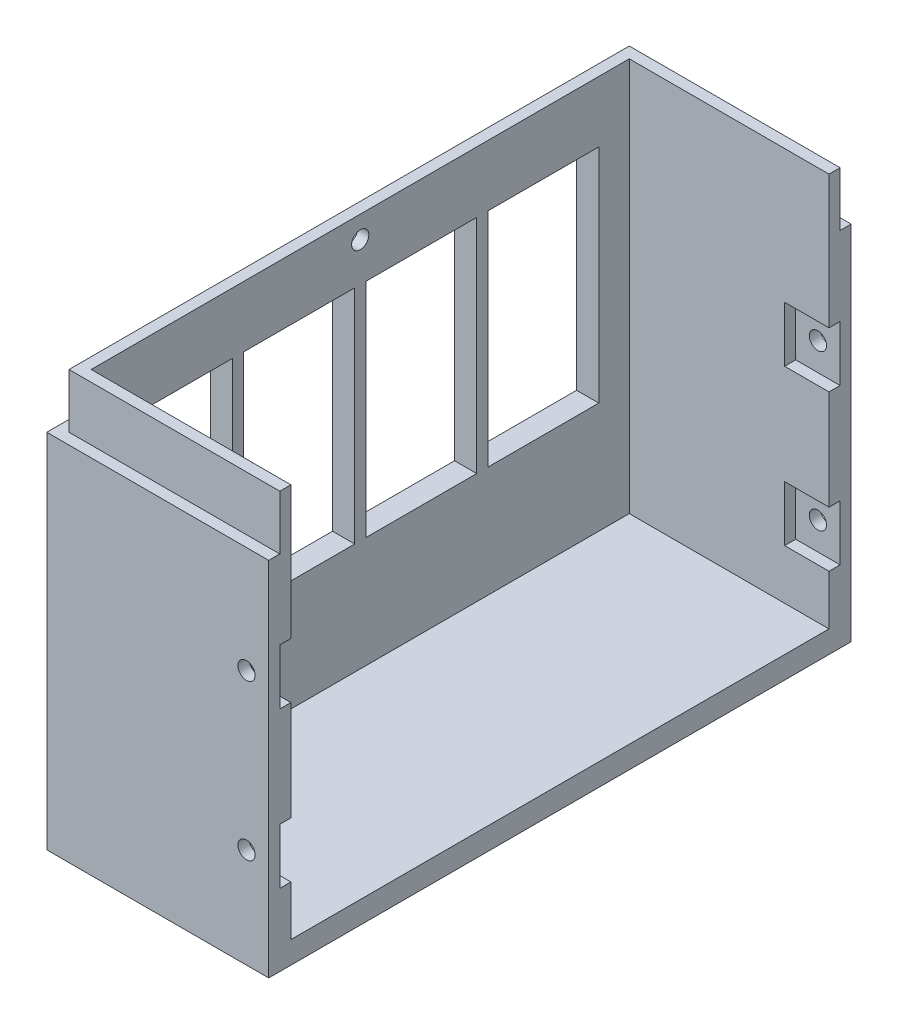
SolidWorks part; units mm, degrees
ref_plane "Front Plane" through (0, 0, 0) normal (0, 0, 1) x (1, 0, 0)
ref_plane "Top Plane" through (0, 0, 0) normal (0, 1, 0) x (1, 0, 0)
ref_plane "Right Plane" through (0, 0, 0) normal (1, 0, 0) x (0, 0, -1)
sketch "Sketch1" plane through (0, 0, 0) normal (0, 1, 0) x (1, 0, 0)
  line L1 (-20, 52.5) -> (20, 52.5)
  line L2 (-20, 52.5) -> (-20, -52.5)
  line L3 (-20, -52.5) -> (20, -52.5)
  line L4 (20, 52.5) -> (20, -52.5)
  line L5 (-20, 52.5) -> (20, -52.5) construction
  line L6 (-20, -52.5) -> (20, 52.5) construction
  point P0 (0, 0)
  dimension "D1" = 105
  dimension "D2" = 40
extrude "Boss-Extrude3" add sketch "Sketch1" along normal blind 75
sketch "Sketch4" plane through (20, 0, 0) normal (1, 0, 0) x (0, 0, -1)
  line L0 (-52.5, 75) -> (52.5, 75) construction
  line L1 (-48.5, 75) -> (48.5, 75)
  line L2 (-48.5, 75) -> (-48.5, 4)
  line L3 (-48.5, 4) -> (48.5, 4)
  line L4 (48.5, 75) -> (48.5, 4)
  line L5 (-52.5, 75) -> (-52.5, 0) construction
  line L6 (-52.5, 0) -> (52.5, 0) construction
  line L7 (52.5, 75) -> (52.5, 0) construction
  dimension "D1" = 4
  dimension "D2" = 4
  dimension "D3" = 4
extrude "Cut-Extrude2" cut sketch "Sketch4" against normal blind 36
sketch "Sketch5" plane through (0, 0, 52.5) normal (0, 0, 1) x (1, 0, 0)
  line L0 (-20, 75) -> (-20, 0) construction
  line L1 (20, 75) -> (-20, 75)
  line L2 (20, 75) -> (20, 65.2)
  line L3 (20, 65.2) -> (-20, 65.2)
  line L4 (-20, 75) -> (-20, 65.2)
  dimension "D1" = 9.8
extrude "Cut-Extrude3" cut sketch "Sketch5" against normal blind 2
sketch "Sketch6" plane through (0, 0, -52.5) normal (0, 0, -1) x (-1, 0, 0)
  line L0 (20, 75) -> (20, 0) construction
  line L1 (-20, 75) -> (20, 75)
  line L2 (-20, 75) -> (-20, 65.2)
  line L3 (-20, 65.2) -> (20, 65.2)
  line L4 (20, 75) -> (20, 65.2)
  dimension "D1" = 9.8
extrude "Cut-Extrude4" cut sketch "Sketch6" against normal blind 2
sketch "Sketch7" plane through (-20, 0, 0) normal (-1, 0, 0) x (0, 0, 1)
  line L1 (-50.5, 75) -> (50.5, 75)
  line L2 (-50.5, 75) -> (-50.5, 65.2)
  line L3 (-50.5, 65.2) -> (50.5, 65.2)
  line L4 (50.5, 75) -> (50.5, 65.2)
extrude "Cut-Extrude5" cut sketch "Sketch7" against normal blind 2
sketch "Sketch8" plane through (0, 0, 48.5) normal (0, 0, -1) x (-1, 0, 0)
  line L0 (-20, 75) -> (-20, 4) construction
  line L1 (16, 4) -> (-20, 4) construction
  circle A0 centre (-16, 18) radius 1.55
  circle A1 centre (-16, 46) radius 1.55
  dimension "D1" = 3.1
  dimension "D2" = 3.1
  dimension "D5" = 14
  dimension "D6" = 28
  dimension "D3" = 4
  dimension "D4" = 4
extrude "Cut-Extrude6" cut sketch "Sketch8" against normal through all and the other way through all
sketch "Sketch9" plane through (0, 0, 48.5) normal (0, 0, -1) x (-1, 0, 0)
  line L0 (-20, 75) -> (-20, 4) construction
  line L1 (-12, 23) -> (-20, 23)
  line L2 (-12, 23) -> (-12, 13)
  line L3 (-12, 13) -> (-20, 13)
  line L4 (-20, 23) -> (-20, 13)
  line L5 (-12, 23) -> (-20, 13) construction
  line L6 (-12, 13) -> (-20, 23) construction
  line L8 (-20, 51) -> (-12, 51)
  line L9 (-20, 51) -> (-20, 41)
  line L10 (-20, 41) -> (-12, 41)
  line L11 (-12, 51) -> (-12, 41)
  line L12 (-20, 51) -> (-12, 41) construction
  line L13 (-20, 41) -> (-12, 51) construction
  point P0 (-16, 18)
  point P8 (-16, 46)
  dimension "D1" = 10
  dimension "D2" = 10
extrude "Cut-Extrude7" cut sketch "Sketch9" against normal blind 2
sketch "Sketch10" plane through (-18, 0, 0) normal (-1, 0, 0) x (0, 0, 1)
  line L0 (50.5, 75) -> (-50.5, 75) construction
  circle A0 centre (0, 71) radius 1.55
  dimension "D1" = 3.1
  dimension "D2" = 4
extrude "Cut-Extrude8" cut sketch "Sketch10" against normal blind 2
sketch "Sketch11" plane through (0, 0, -48.5) normal (0, 0, 1) x (1, 0, 0)
  line L0 (20, 4) -> (20, 75) construction
  line L1 (12, 51) -> (20, 51)
  line L2 (12, 51) -> (12, 41)
  line L3 (12, 41) -> (20, 41)
  line L4 (20, 51) -> (20, 41)
  line L5 (12, 51) -> (20, 41) construction
  line L6 (12, 41) -> (20, 51) construction
  line L8 (12, 23) -> (20, 23)
  line L9 (12, 23) -> (12, 13)
  line L10 (12, 13) -> (20, 13)
  line L11 (20, 23) -> (20, 13)
  line L12 (12, 23) -> (20, 13) construction
  line L13 (12, 13) -> (20, 23) construction
  point P0 (16, 46)
  point P8 (16, 18)
  dimension "D1" = 8
  dimension "D2" = 10
  dimension "D3" = 10
extrude "Cut-Extrude9" cut sketch "Sketch11" against normal blind 2
sketch "Sketch12" plane through (-20, 0, 0) normal (-1, 0, 0) x (0, 0, 1)
  line L0 (-52.5, 0) -> (52.5, 0) construction
  line L1 (-43, 64) -> (-23, 64)
  line L2 (-43, 64) -> (-43, 24)
  line L3 (-43, 24) -> (-23, 24)
  line L4 (-23, 64) -> (-23, 24)
  line L5 (-21, 64) -> (-1, 64)
  line L6 (-21, 64) -> (-21, 24)
  line L7 (-21, 24) -> (-1, 24)
  line L8 (-1, 64) -> (-1, 24)
  line L9 (1, 64) -> (21, 64)
  line L10 (1, 64) -> (1, 24)
  line L11 (1, 24) -> (21, 24)
  line L12 (21, 64) -> (21, 24)
  line L13 (23, 64) -> (43, 64)
  line L14 (23, 64) -> (23, 24)
  line L15 (23, 24) -> (43, 24)
  line L16 (43, 64) -> (43, 24)
  line L17 (-52.5, 65.2) -> (-52.5, 0) construction
  dimension "D1" = 20
  dimension "D2" = 40
  dimension "D3" = 20
  dimension "D4" = 40
  dimension "D5" = 20
  dimension "D6" = 40
  dimension "D7" = 20
  dimension "D8" = 40
  dimension "D9" = 24
  dimension "D10" = 2
  dimension "D11" = 2
  dimension "D12" = 2
  dimension "D13" = 9.5
extrude "Cut-Extrude10" cut sketch "Sketch12" against normal up to next
